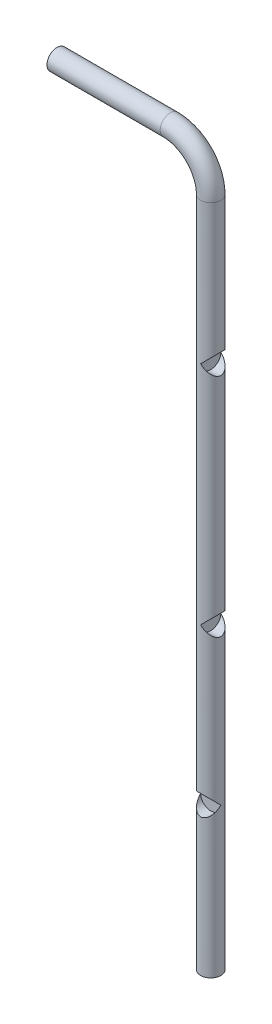
SolidWorks part; units mm, degrees
ref_plane "Front Plane" through (0, 0, 0) normal (0, 0, 1) x (1, 0, 0)
ref_plane "Top Plane" through (0, 0, 0) normal (0, 1, 0) x (1, 0, 0)
ref_plane "Right Plane" through (0, 0, 0) normal (1, 0, 0) x (0, 0, -1)
sketch "Sketch1" plane through (0, 0, 0) normal (0, 0, 1) x (1, 0, 0)
  line L0 (0, 0) -> (0, 830)
  line L1 (-50, 880) -> (-190, 880)
  arc A0 (0, 830) -> (-50, 880) centre (-50, 830) ccw
  dimension "D2" = 50
  dimension "D1" = 830
  dimension "D3" = 140
sweep "Sweep1" add path "Sketch1" circular profile diameter 25 parameters "D3"=25
sketch "Sketch2" plane through (0, 0, 0) normal (0, 0, 1) x (1, 0, 0)
  line L0 (0, 0) -> (0, 182.5) construction
  circle A0 centre (0, 182.5) radius 12.5
  dimension "D2" = 25
  dimension "D1" = 182.5
sketch "Sketch8" plane through (0, 0, 0) normal (1, 0, 0) x (0, 0, -1)
  line L0 (0, 830) -> (0, 655.01) construction
  line L1 (12.5, 830) -> (-12.5, 830) construction
  line L2 (0, 655.01) -> (0, 375.5) construction
  circle A0 centre (0, 655.01) radius 12.5
  circle A1 centre (0, 375.5) radius 12.5
  dimension "D2" = 25
  dimension "D4" = 25
  dimension "D1" = 174.99
  dimension "D3" = 279.51
extrude "Cut-Extrude3" cut sketch "Sketch8" along normal blind 21
extrude "Cut-Extrude6" cut sketch "Sketch2" along normal blind 13
